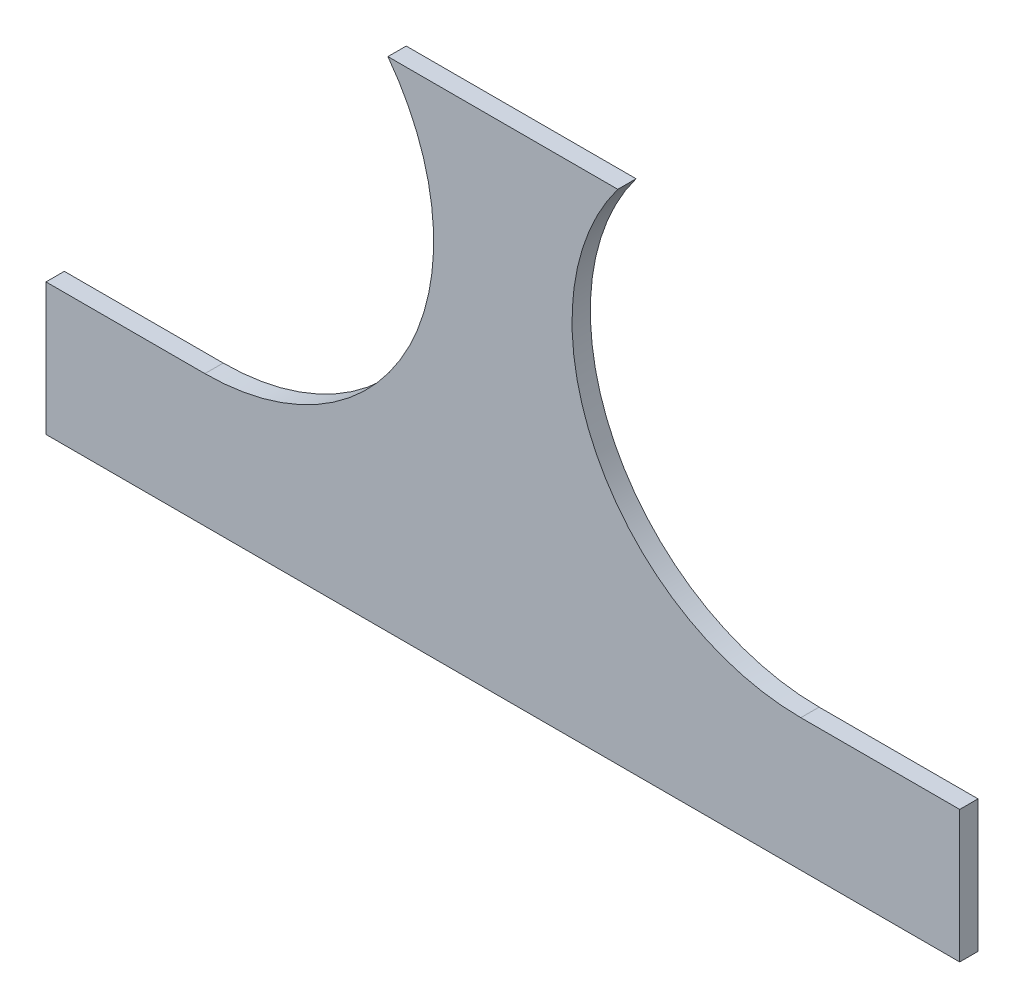
SolidWorks part; units mm, degrees
ref_plane "Front Plane" through (0, 0, 0) normal (0, 0, 1) x (1, 0, 0)
ref_plane "Top Plane" through (0, 0, 0) normal (0, 1, 0) x (1, 0, 0)
ref_plane "Right Plane" through (0, 0, 0) normal (1, 0, 0) x (0, 0, -1)
sketch "Sketch1" plane through (0, 0, 0) normal (0, 0, 1) x (1, 0, 0)
  line L0 (124.8, 0) -> (124.8, -267.4) construction
  line L1 (0, 0) -> (249.6, 0)
  line L2 (0, 0) -> (0, -267.4)
  line L3 (0, -267.4) -> (249.6, -267.4)
  line L4 (249.6, 0) -> (249.6, -267.4)
  line L7 (249.6, -267.4) -> (249.6, -100) construction
  line L8 (249.6, -267.4) -> (0, -267.4) construction
extrude "Boss-Extrude1" add sketch "Sketch1" along normal blind 5
sketch "Sketch5" plane through (0, 0, 5) normal (0, 0, 1) x (1, 0, 0)
  line L4 (0, -136.0954) -> (249.6, -136.0954)
  line L15 (249.6, 25) -> (249.6, -100) construction
  line L17 (249.6, 25) -> (206.1971, 25)
  line L19 (206.1971, 25) -> (249.6, 25) construction
  line L20 (249.6, -100) -> (206.1971, -100)
  line L26 (249.6, -267.4) -> (249.6, 0) construction
  line L27 (0, -100) -> (249.6, -100) construction
  line L28 (0, 25) -> (0, -100)
  line L29 (0, -136.0954) -> (0, -267.4)
  line L30 (0, -267.4) -> (249.6, -267.4)
  line L31 (249.6, -267.4) -> (249.6, -136.0954)
  line L32 (249.6, 25) -> (249.6, -100)
  line L33 (0, -100) -> (43.4029, -100)
  line L35 (0, 25) -> (43.4029, 25)
  line L36 (43.4029, 25) -> (0, 25) construction
  line L37 (0, 25) -> (0, -100) construction
  line L39 (64.8, -136.0954) -> (59.8, -136.0954) construction
  arc A7 (206.1971, 25) -> (206.1971, -100) centre (206.1971, -37.5) ccw
  arc A8 (206.1971, 25) -> (206.1971, -100) centre (206.1971, -37.5) ccw construction
  arc A9 (43.4029, 25) -> (43.4029, -100) centre (43.4029, -37.5) cw
  arc A10 (43.4029, -100) -> (43.4029, 25) centre (43.4029, -37.5) ccw construction
extrude "Cut-Extrude3" cut sketch "Sketch5" against normal through all
